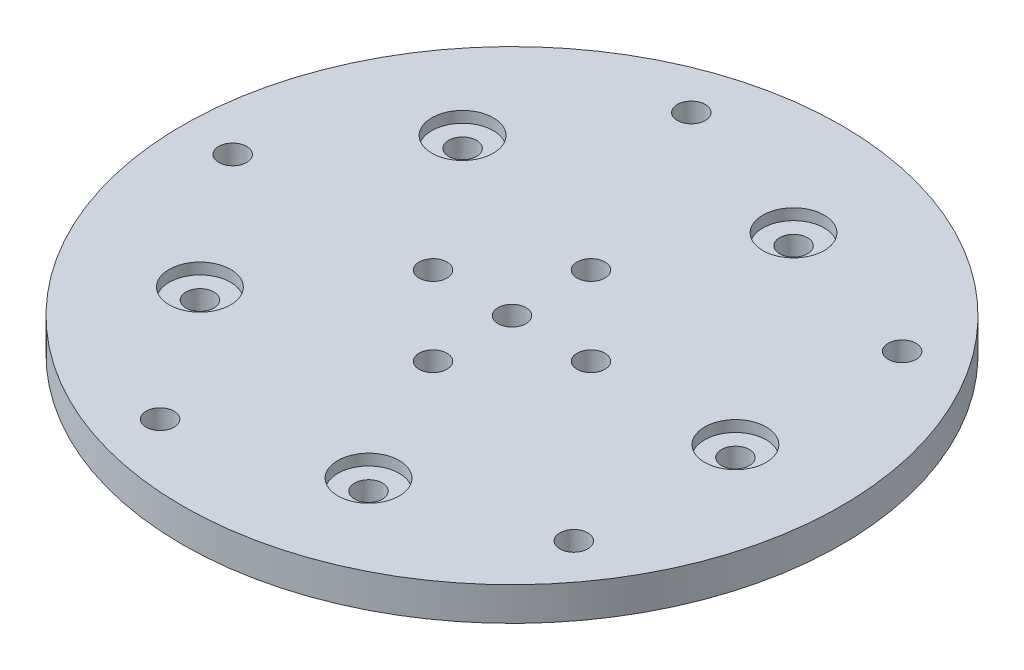
SolidWorks part; units mm, degrees
ref_plane "前视基准面" through (0, 0, 0) normal (0, 0, 1) x (1, 0, 0)
ref_plane "上视基准面" through (0, 0, 0) normal (0, 1, 0) x (1, 0, 0)
ref_plane "右视基准面" through (0, 0, 0) normal (1, 0, 0) x (0, 0, -1)
other "Configuration Table"
sketch "草图1" plane through (0, 0, 0) normal (0, 1, 0) x (1, 0, 0)
  circle A0 centre (0, 0) radius 29.5
  dimension "D1" = 59
extrude "凸台-拉伸1" add sketch "草图1" along normal blind 3
sketch "草图2" plane through (0, 3, 0) normal (0, 1, 0) x (1, 0, 0)
  line L0 (0, 0) -> (39.3262, 0) construction
  circle A0 centre (0, 0) radius 27.5 construction
  circle A1 centre (20, 0) radius 1.5
  circle A2 centre (6.1803, -19.0211) radius 1.5
  circle A3 centre (-16.1803, -11.7557) radius 1.5
  circle A4 centre (-16.1803, 11.7557) radius 1.5
  circle A5 centre (6.1803, 19.0211) radius 1.5
  point P3 (20, 0)
  point P9 (6.1803, -19.0211)
  point P11 (-16.1803, -11.7557)
  point P13 (-16.1803, 11.7557)
  point P15 (6.1803, 19.0211)
  point P17 (0, 0)
  point P18 (0, 0)
  dimension "D1" = 55
  dimension "D3" = 5
  dimension "D4" = 3
  dimension "D2" = 20
hole_wizard "M3 螺纹孔4" positions "草图2" profile "草图4" tap size "M3" standard "GB"
sketch "草图4" plane through (6.1803, 3, -19.0211) normal (1, 0, 0) x (0, 0, 1)
  line L0 (0, 0) -> (0, 3)
  line L1 (0, 3) -> (1.25, 3)
  line L2 (1.25, 3) -> (1.25, 0)
  line L5 (1.25, 0) -> (0, 0)
  line L11 (0, -6.35) -> (0, 107.95) construction
  dimension "通孔螺纹孔钻头直径" = 2.5
  dimension "通孔螺纹孔钻头深度" = 3
sketch "草图5" plane through (0, 3, 0) normal (0, 1, 0) x (1, 0, 0)
  line L0 (0, 0) -> (-39.7998, 0) construction
  circle A0 centre (-25, 0) radius 1.5
  circle A1 centre (-7.7254, 23.7764) radius 1.5
  circle A2 centre (20.2254, 14.6946) radius 1.5
  circle A3 centre (20.2254, -14.6946) radius 1.5
  circle A4 centre (-7.7254, -23.7764) radius 1.5
  circle A5 centre (-7.0711, 0) radius 1.5
  circle A6 centre (0, 7.0711) radius 1.5
  circle A7 centre (7.0711, 0) radius 1.5
  circle A8 centre (0, -7.0711) radius 1.5
  point P3 (-25, 0)
  point P6 (-7.0711, 0)
  point P8 (-7.7254, 23.7764)
  point P10 (20.2254, 14.6946)
  point P12 (20.2254, -14.6946)
  point P14 (-7.7254, -23.7764)
  point P16 (0, 0)
  point P19 (0, 7.0711)
  point P21 (7.0711, 0)
  point P23 (0, -7.0711)
  point P25 (0, 0)
  point P44 (20.2254, -14.6946)
  dimension "D2" = 3
  dimension "D5" = 3
  dimension "D1" = 25
  dimension "D6" = 10
  dimension "D3" = 5
  dimension "D4" = 4
hole_wizard "M3 螺纹孔1" positions "草图5" profile "草图7" tap size "M3" standard "GB" end condition through all
sketch "草图7" plane through (20.2254, 3, 14.6946) normal (1, 0, 0) x (0, 0, 1)
  line L0 (0, 0) -> (0, 3)
  line L1 (0, 3) -> (1.25, 3)
  line L2 (1.25, 3) -> (1.25, 0)
  line L5 (1.25, 0) -> (0, 0)
  line L11 (0, -6.35) -> (0, 107.95) construction
  dimension "通孔螺纹孔钻头直径" = 2.5
  dimension "通孔螺纹孔钻头深度" = 3
cosmetic thread "孔螺蚊线1" parameters "D2"=3
cosmetic thread "孔螺蚊线2" parameters "D2"=3
cosmetic thread "孔螺蚊线3" parameters "D2"=3
cosmetic thread "孔螺蚊线4" parameters "D2"=3
cosmetic thread "孔螺蚊线5" parameters "D2"=3
cosmetic thread "孔螺蚊线6" parameters "D2"=3
cosmetic thread "孔螺蚊线7" parameters "D2"=3
cosmetic thread "孔螺蚊线8" parameters "D2"=3
cosmetic thread "孔螺蚊线9" parameters "D2"=3
cosmetic thread "孔螺蚊线10" parameters "D2"=3
sketch "草图9" plane through (0, 3, 0) normal (0, 1, 0) x (1, 0, 0)
  line L0 (0, 0) -> (31.7949, 0) construction
  circle A0 centre (0, 0) radius 27.5 construction
  circle A1 centre (20, 0) radius 2.75
  circle A2 centre (6.1803, -19.0211) radius 2.75
  circle A3 centre (-16.1803, -11.7557) radius 2.75
  circle A4 centre (-16.1803, 11.7557) radius 2.75
  circle A5 centre (6.1803, 19.0211) radius 2.75
  point P3 (20, 0)
  point P6 (-3.31, 3.6566)
  point P7 (0, 0)
  point P9 (6.1803, -19.0211)
  point P11 (-16.1803, -11.7557)
  point P13 (-16.1803, 11.7557)
  point P15 (6.1803, 19.0211)
  point P17 (0, 0)
  dimension "D1" = 55
  dimension "D3" = 5
  dimension "D4" = 5.5
  dimension "D2" = 20
extrude "切除-拉伸1" cut sketch "草图9" against normal blind 1 and the other way through all
